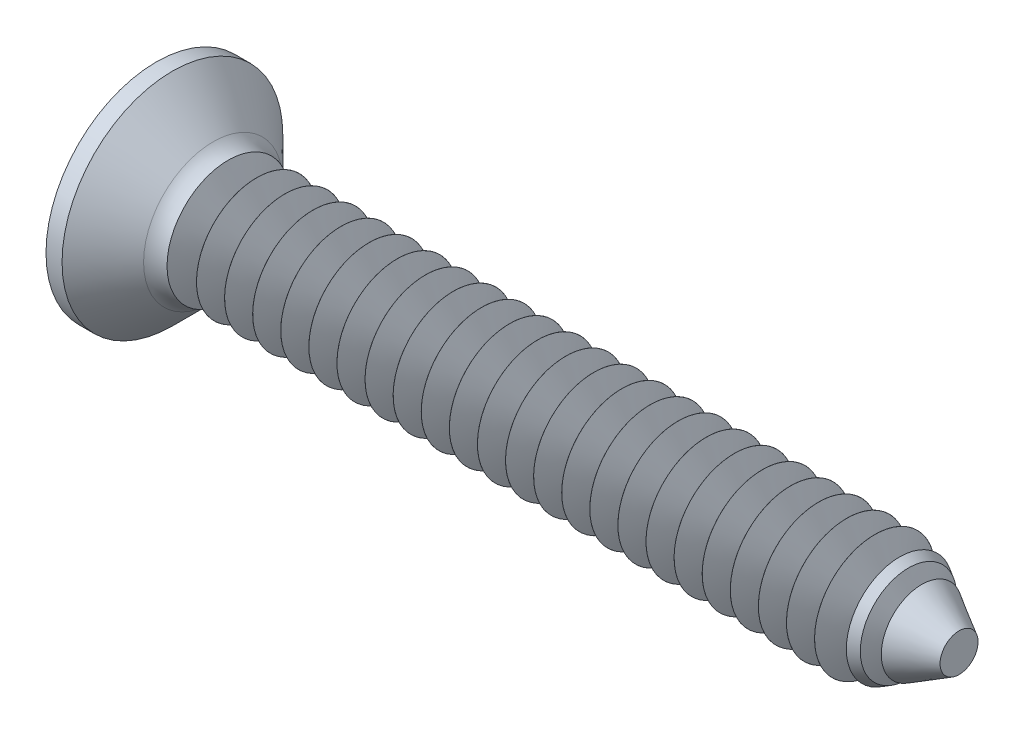
SolidWorks part; units mm, degrees
ref_plane "Plane1" through (0, 0, 0) normal (0, 0, 1) x (1, 0, 0)
ref_plane "Plane2" through (0, 0, 0) normal (0, 1, 0) x (1, 0, 0)
ref_plane "Plane3" through (0, 0, 0) normal (1, 0, 0) x (0, 0, -1)
sketch "BodySke" plane through (0, 0, 0) normal (0, 0, 1) x (1, 0, 0)
  line L0 (0, 0) -> (0, 2.75)
  line L1 (0, 2.75) -> (0.4, 2.75)
  line L2 (1.65, 1.5) -> (18.2209, 1.5)
  line L3 (20, 0.4728) -> (20, 0)
  line L4 (20, 0) -> (0, 0)
  line L5 (-6.35, 0) -> (82.55, 0) construction
  line L6 (1.65, -1.5) -> (25, -1.5) construction
  line L7 (0.4, -2.75) -> (1.65, -1.5) construction
  line L8 (0.4, 2.75) -> (1.65, 1.5)
  line L9 (0, -2.75) -> (0.4, -2.75) construction
  line L10 (2.15, 3.0875) -> (2.15, -6.4375) construction
  line L11 (0, 6.35) -> (0, -3.175) construction
  line L12 (20, 0.4728) -> (18.2209, 1.5)
  dimension "D1" = 20
  dimension "Diameter" = 3
  dimension "D2" = 30
  dimension "Head_ht" = 1.65
  dimension "Head_dia" = 5.5
  dimension "Head_ang" = 90
  dimension "D6" = 0.4
  dimension "Advance" = 0.5
revolve "Base-Revolve" add sketch "BodySke"
cosmetic thread "ThreadCosmetic"
fillet "Fillet1" radius 0.8 1 edges at (1.65, 0, 1.5)
sketch "Sketch3" plane through (0, 0, 0) normal (-1, 0, 0) x (0, 0, 1)
  line L0 (-0.37, 1.5) -> (0.37, 1.5)
  line L1 (0.37, 1.5) -> (0.37, -1.5)
  line L2 (0.37, -1.5) -> (-0.37, -1.5)
  line L3 (-0.37, -1.5) -> (-0.37, 1.5)
  dimension "D1" = 1.5
  dimension "Cross_dia" = 3
  dimension "D2" = 0.37
  dimension "Cross_width" = 0.74
ref_plane "Plane4" through (2.01, 0, 0) normal (-1, 0, 0) x (0, 0, 1)
sketch "Sketch4" plane through (2.01, 0, 0) normal (-1, 0, 0) x (0, 0, 1)
  line L0 (-0.37, 0.4979) -> (0.37, 0.4979)
  line L3 (0.37, 0.4979) -> (0.37, -0.4979)
  line L4 (0.37, -0.4979) -> (-0.37, -0.4979)
  line L5 (-0.37, -0.4979) -> (-0.37, 0.4979)
  dimension "D1" = 0.74
  dimension "D2" = 0.9957
  dimension "D3" = 0.37
  dimension "D4" = 0.4979
loft "Recess" cut profiles "Sketch3", "Sketch4"
pattern_circular "RecPat" count 2 every 90 about axis through (0, 0, 0) along (1, 0, 0) of "Recess"
sketch "RecCorSke" plane through (0, 0, 0) normal (0, 0, 1) x (1, 0, 0)
  line L0 (-3.175, 0) -> (15.875, 0) construction
  line L2 (0, 0) -> (0, 0.6966)
  line L3 (0, 0.6966) -> (2.01, 0.556)
  line L4 (2.01, 0.556) -> (2.1907, 0)
  line L5 (2.1907, 0) -> (0, 0)
  dimension "Diameter" = 1.112
  dimension "Depth" = 2.01
  dimension "Draft_angle" = 4
  dimension "Bottom_angle" = 18
revolve "RecessCore" cut sketch "RecCorSke" angle 360 about L0
sketch "ThdSchSke" plane through (0, 0, 0) normal (0, 0, 1) x (1, 0, 0)
  line L0 (2.15, -0.75) -> (1.5671, -2)
  line L1 (2.15, -0.75) -> (2.7329, -2)
  line L2 (2.7329, -2) -> (2.7329, -3)
  line L3 (-3.175, 0) -> (5.1513, 0) construction
  line L5 (2.7329, -3) -> (1.5671, -3)
  line L6 (1.5671, -3) -> (1.5671, -2)
  line L7 (0, 2.75) -> (0, -2.75) construction
  dimension "D1" = 4
  dimension "D2" = 50
  dimension "D3" = 1.5
  dimension "Start" = 2.15
  dimension "D4" = 65
revolve "ThreadSchematic" cut sketch "ThdSchSke" angle 360 about L3
pattern_linear "ThdSchPat" count 25 spacing 0.7 along (1, 0, 0) of "ThreadSchematic"
